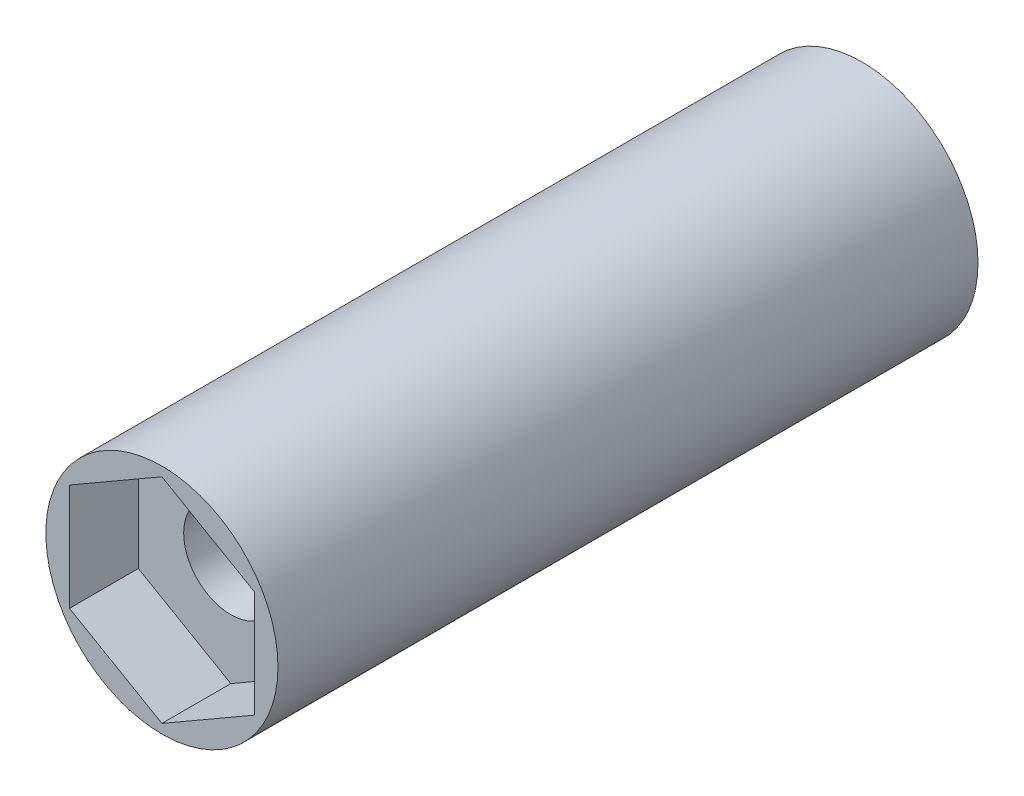
SolidWorks part; units mm, degrees
ref_plane "Front Plane" through (0, 0, 0) normal (0, 0, 1) x (1, 0, 0)
ref_plane "Top Plane" through (0, 0, 0) normal (0, 1, 0) x (1, 0, 0)
ref_plane "Right Plane" through (0, 0, 0) normal (1, 0, 0) x (0, 0, -1)
sketch "Sketch1" plane through (0, 0, 0) normal (0, 0, 1) x (1, 0, 0)
  circle A0 centre (-32.2, 44.45) radius 2.929
  circle A1 centre (-32.2, 44.45) radius 3.2
  dimension "D1" = 0.1
  dimension "D2" = 6.4
extrude "Boss-Extrude1" add sketch "Sketch1" along normal blind 2.2
sketch "Sketch2" plane through (0, 0, 2.2) normal (0, 0, 1) x (1, 0, 0)
  circle A0 centre (-32.2, 44.45) radius 3.2 construction
  circle A1 centre (-32.2, 44.45) radius 3.2
  circle A2 centre (-32.2, 44.45) radius 1.3
  dimension "D1" = 2.6
extrude "Boss-Extrude2" add sketch "Sketch2" along normal up to surface (15.2 mm away)
sketch "Sketch3" plane through (0, 0, 17.4) normal (0, 0, 1) x (1, 0, 0)
  line L12 (-34.75, 42.9778) -> (-32.2, 41.5055)
  line L13 (-32.2, 41.5055) -> (-29.65, 42.9778)
  line L14 (-29.65, 42.9778) -> (-29.65, 45.9222)
  line L15 (-29.65, 45.9222) -> (-32.2, 47.3945)
  line L16 (-32.2, 47.3945) -> (-34.75, 45.9222)
  line L17 (-34.75, 45.9222) -> (-34.75, 42.9778)
  line L18 (-34.75, 42.9778) -> (-32.2, 41.5055)
  line L19 (-32.2, 41.5055) -> (-29.65, 42.9778)
  line L20 (-29.65, 42.9778) -> (-29.65, 45.9222)
  line L21 (-29.65, 45.9222) -> (-32.2, 47.3945)
  line L22 (-32.2, 47.3945) -> (-34.75, 45.9222)
  line L23 (-34.75, 45.9222) -> (-34.75, 42.9778)
  circle A0 centre (-32.2, 44.45) radius 3.2 construction
  circle A1 centre (-32.2, 44.45) radius 3.2
  dimension "D1" = 0.1
extrude "Boss-Extrude3" add sketch "Sketch3" along normal up to surface (1.9 mm away)
sketch "Sketch4" plane through (0, 0, 2.2) normal (0, 0, -1) x (-1, 0, 0)
  circle A0 centre (32.2, 44.45) radius 1.3 construction
  circle A1 centre (32.2, 44.45) radius 1.3
extrude "Boss-Extrude4" add sketch "Sketch4" against normal blind 0.2
